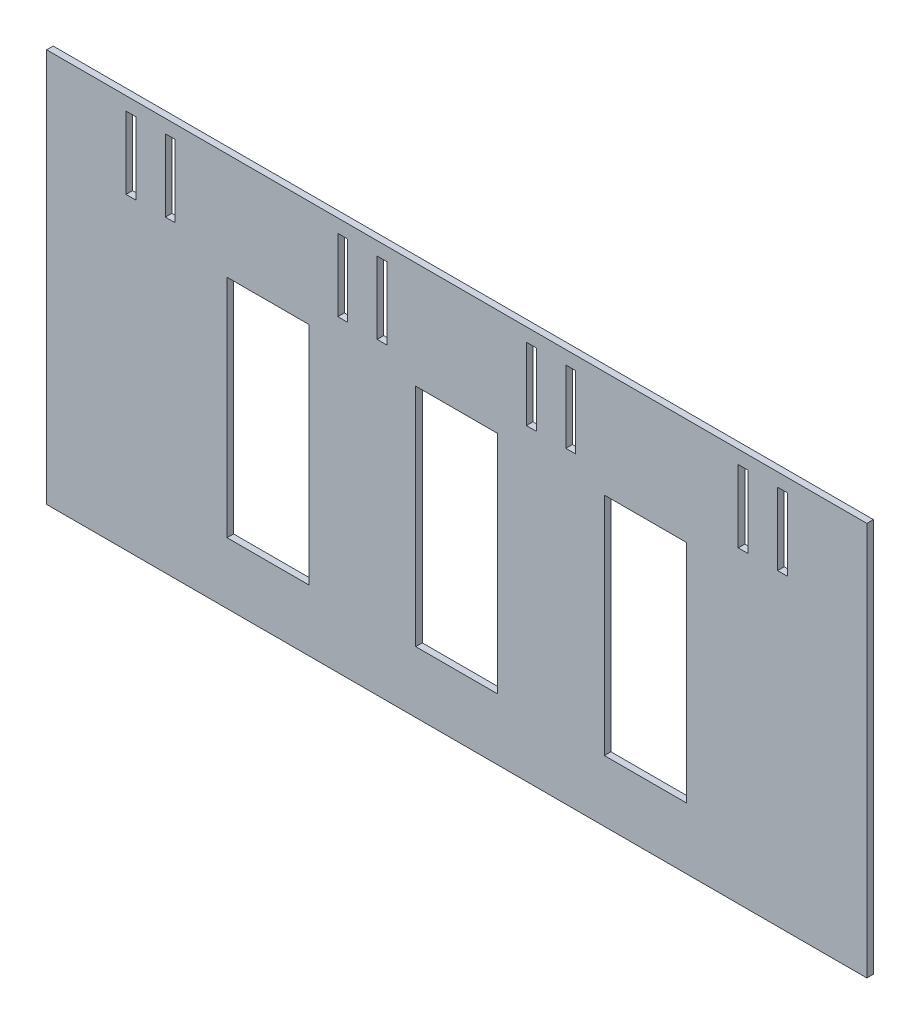
SolidWorks part; units mm, degrees
material "AISI 304"
ref_plane "前视基准面" through (0, 0, 0) normal (0, 0, 1) x (1, 0, 0)
ref_plane "上视基准面" through (0, 0, 0) normal (0, 1, 0) x (1, 0, 0)
ref_plane "右视基准面" through (0, 0, 0) normal (1, 0, 0) x (0, 0, -1)
sketch "草图1" plane through (0, 0, 0) normal (0, 0, 1) x (1, 0, 0)
  line L1 (-39.4185, 132.6579) -> (210.5815, 132.6579)
  line L2 (-39.4185, 132.6579) -> (-39.4185, 12.6579)
  line L3 (-39.4185, 12.6579) -> (210.5815, 12.6579)
  line L4 (210.5815, 132.6579) -> (210.5815, 12.6579)
extrude "凸台-拉伸1" add sketch "草图1" along normal blind 2
sketch "草图2" plane through (0, 0, 2) normal (0, 0, 1) x (1, 0, 0)
  line L0 (-39.4185, 132.6579) -> (-39.4185, 12.6579) construction
  line L1 (-15.2185, 128.5929) -> (-12.2185, 128.5929)
  line L2 (-15.2185, 128.5929) -> (-15.2185, 106.5929)
  line L3 (-15.2185, 106.5929) -> (-12.2185, 106.5929)
  line L4 (-12.2185, 128.5929) -> (-12.2185, 106.5929)
  line L5 (-3.2185, 128.5929) -> (-0.2185, 128.5929)
  line L6 (-3.2185, 128.5929) -> (-3.2185, 106.5929)
  line L7 (-3.2185, 106.5929) -> (-0.2185, 106.5929)
  line L8 (-0.2185, 128.5929) -> (-0.2185, 106.5929)
  line L9 (49.3315, 128.5929) -> (52.3315, 128.5929)
  line L10 (49.3315, 128.5929) -> (49.3315, 106.5929)
  line L11 (49.3315, 106.5929) -> (52.3315, 106.5929)
  line L12 (52.3315, 128.5929) -> (52.3315, 106.5929)
  line L13 (61.3315, 128.5929) -> (64.3315, 128.5929)
  line L14 (61.3315, 128.5929) -> (61.3315, 106.5929)
  line L15 (61.3315, 106.5929) -> (64.3315, 106.5929)
  line L16 (64.3315, 128.5929) -> (64.3315, 106.5929)
  line L17 (106.8315, 128.5929) -> (109.8315, 128.5929)
  line L18 (106.8315, 128.5929) -> (106.8315, 106.5929)
  line L19 (106.8315, 106.5929) -> (109.8315, 106.5929)
  line L20 (109.8315, 128.5929) -> (109.8315, 106.5929)
  line L21 (118.8315, 128.5929) -> (121.8315, 128.5929)
  line L22 (118.8315, 128.5929) -> (118.8315, 106.5929)
  line L23 (118.8315, 106.5929) -> (121.8315, 106.5929)
  line L24 (121.8315, 128.5929) -> (121.8315, 106.5929)
  line L25 (171.3815, 128.5929) -> (174.3815, 128.5929)
  line L26 (171.3815, 128.5929) -> (171.3815, 106.5929)
  line L27 (171.3815, 106.5929) -> (174.3815, 106.5929)
  line L28 (174.3815, 128.5929) -> (174.3815, 106.5929)
  line L29 (183.3815, 128.5929) -> (186.3815, 128.5929)
  line L30 (183.3815, 128.5929) -> (183.3815, 106.5929)
  line L31 (183.3815, 106.5929) -> (186.3815, 106.5929)
  line L32 (186.3815, 128.5929) -> (186.3815, 106.5929)
  line L33 (210.5815, 12.6579) -> (210.5815, 132.6579) construction
  point P34 (-13.7185, 128.5929)
  point P35 (-1.7185, 128.5929)
  point P36 (50.8315, 128.5929)
  point P37 (62.8315, 128.5929)
  point P38 (108.3315, 128.5929)
  point P39 (120.3315, 128.5929)
  point P40 (172.8815, 128.5929)
  point P41 (184.8815, 128.5929)
  dimension "D1" = 24.2
  dimension "D2" = 12
  dimension "D3" = 12
  dimension "D4" = 12
  dimension "D5" = 12
  dimension "D6" = 90.25
  dimension "D7" = 25.7
  dimension "D8" = 90.25
extrude "切除-拉伸1" cut sketch "草图2" against normal blind 2
sketch "草图4" plane through (0, 0, 0) normal (0, 0, -1) x (-1, 0, 0)
  line L0 (-130.5815, 117.005) -> (-130.5815, 58.5885) construction
  line L1 (-155.5815, 31.3702) -> (-130.5815, 31.3702)
  line L2 (-155.5815, 31.3702) -> (-155.5815, 100.1276)
  line L3 (-155.5815, 100.1276) -> (-130.5815, 100.1276)
  line L4 (-130.5815, 31.3702) -> (-130.5815, 100.1276)
  line L5 (-73.0815, 117.005) -> (-73.0815, 58.5885) construction
  line L6 (-98.0815, 31.3702) -> (-73.0815, 31.3702)
  line L7 (-98.0815, 31.3702) -> (-98.0815, 100.1276)
  line L8 (-98.0815, 100.1276) -> (-73.0815, 100.1276)
  line L9 (-73.0815, 31.3702) -> (-73.0815, 100.1276)
  line L10 (-15.5815, 117.005) -> (-15.5815, 58.5885) construction
  line L11 (-40.5815, 31.3702) -> (-15.5815, 31.3702)
  line L12 (-40.5815, 31.3702) -> (-40.5815, 100.1276)
  line L13 (-40.5815, 100.1276) -> (-15.5815, 100.1276)
  line L14 (-15.5815, 31.3702) -> (-15.5815, 100.1276)
  line L15 (-210.5815, 132.6579) -> (39.4185, 132.6579) construction
  dimension "D1" = 25
  dimension "D2" = 68.7574
  dimension "D3" = 32.5303
  dimension "D4" = 25
  dimension "D5" = 25
extrude "切除-拉伸3" cut sketch "草图4" against normal blind 10
